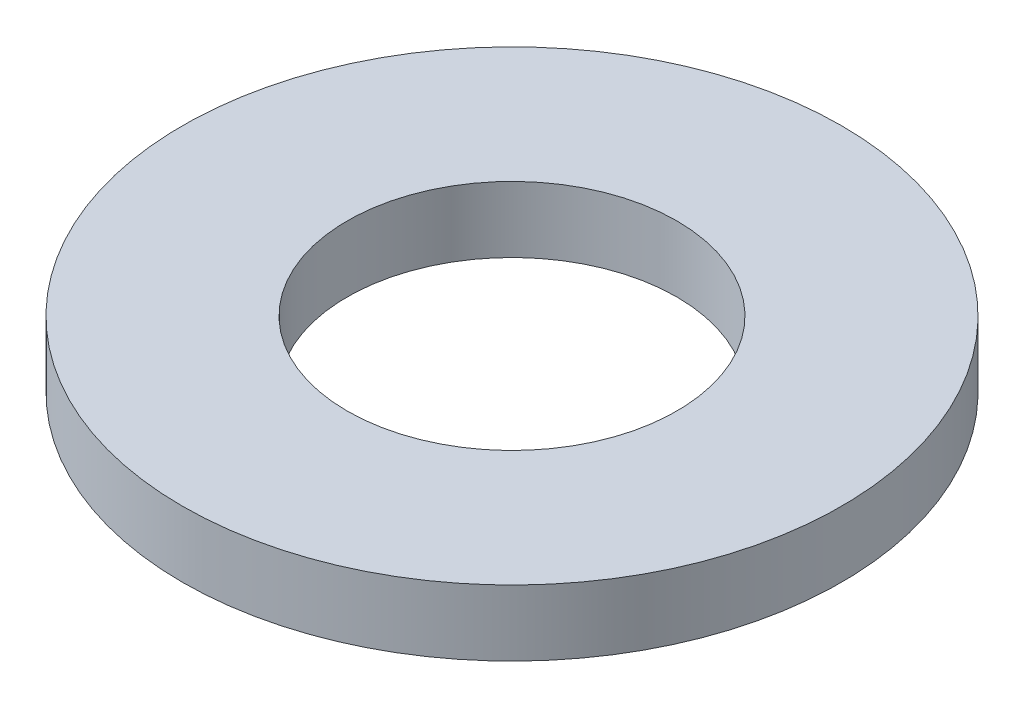
SolidWorks part; units mm, degrees
ref_plane "Front Plane" through (0, 0, 0) normal (0, 0, 1) x (1, 0, 0)
ref_plane "Top Plane" through (0, 0, 0) normal (0, 1, 0) x (1, 0, 0)
ref_plane "Right Plane" through (0, 0, 0) normal (1, 0, 0) x (0, 0, -1)
sketch "Sketch1" plane through (0, 0, 0) normal (0, 1, 0) x (1, 0, 0)
  circle A0 centre (0, 0) radius 5
  circle A1 centre (0, 0) radius 2.5
extrude "Boss-Extrude1" add sketch "Sketch1" along normal blind 1
